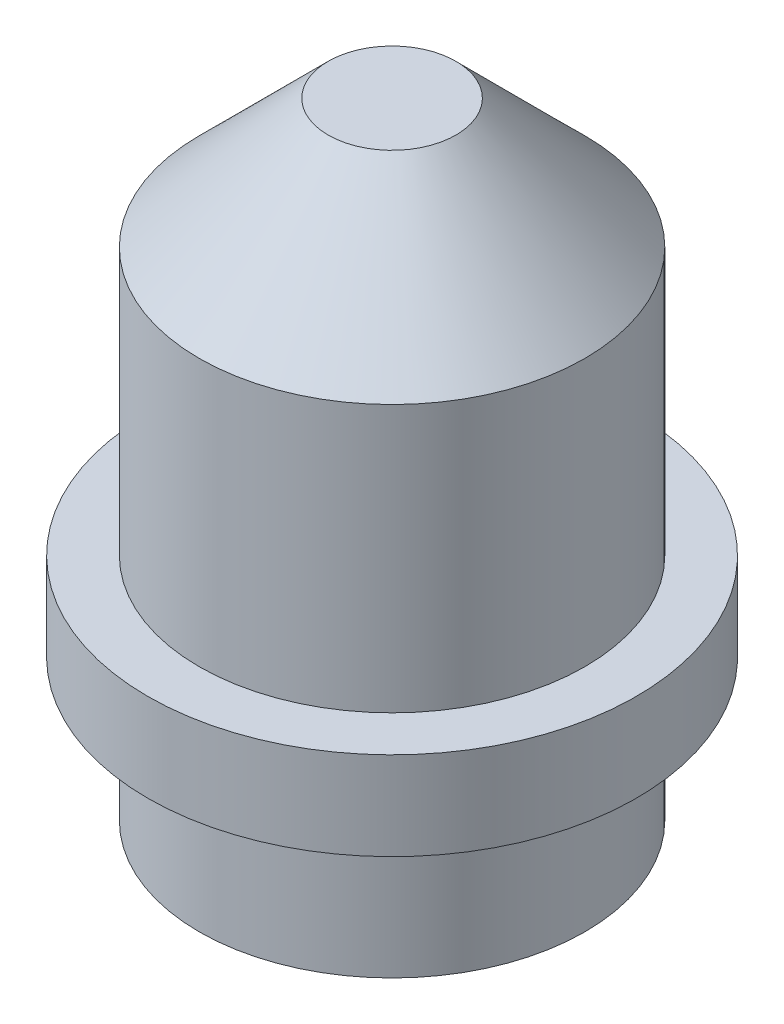
SolidWorks part; units mm, degrees
ref_plane "Спереди" through (0, 0, 0) normal (0, 0, 1) x (1, 0, 0)
ref_plane "Сверху" through (0, 0, 0) normal (0, 1, 0) x (1, 0, 0)
ref_plane "Справа" through (0, 0, 0) normal (1, 0, 0) x (0, 0, -1)
sketch "Эскиз1" plane through (0, 0, 0) normal (0, 0, 1) x (1, 0, 0)
  line L1 (-3.8, 3.572) -> (-3.8, 2.2)
  line L2 (-3.8, 2.2) -> (-3, 2.2)
  line L3 (-3, 2.2) -> (-3, 0)
  line L5 (0, 9.7313) -> (-0.9939, 9.7313)
  line L7 (-3, 0) -> (0, 0)
  line L9 (0, 14.588) -> (0, -0.8473) construction
  line L10 (0, 9.7313) -> (0, 0)
  line L11 (-0.9939, 9.7313) -> (-3, 7.7252)
  line L12 (-3, 7.7252) -> (-3, 3.572)
  line L13 (-3, 3.572) -> (-3.8, 3.572)
  point P8 (0, 0)
  point P10 (0, 0)
revolve "Повернуть1" add sketch "Эскиз1" angle 360 about L9
